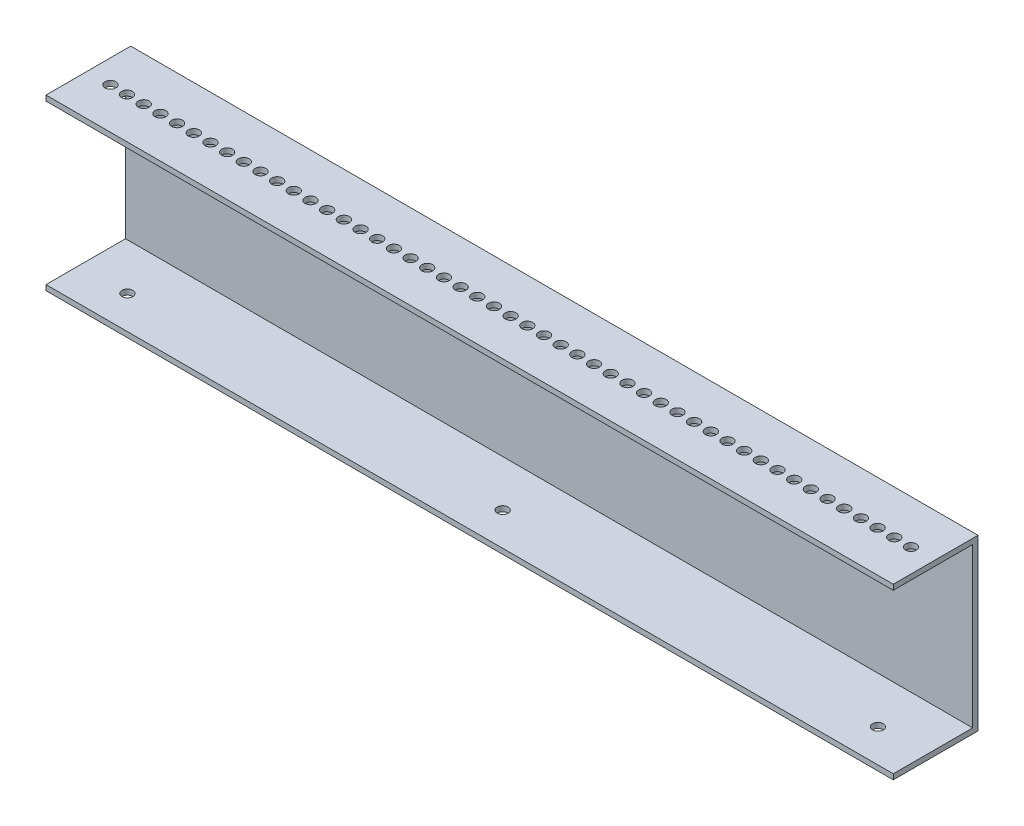
SolidWorks part; units mm, degrees
material "6061-T6 (SS)"
ref_plane "Front Plane" through (0, 0, 0) normal (0, 0, 1) x (1, 0, 0)
ref_plane "Top Plane" through (0, 0, 0) normal (0, 1, 0) x (1, 0, 0)
ref_plane "Right Plane" through (0, 0, 0) normal (1, 0, 0) x (0, 0, -1)
sketch "Sketch3" plane through (0, 0, 0) normal (1, 0, 0) x (0, 0, -1)
  line L0 (-304.8, 12.7) -> (-254, 12.7)
  line L2 (-254, 12.7) -> (-254, 114.3)
  line L4 (-254, 114.3) -> (-304.8, 114.3)
  line L5 (-304.8, 114.3) -> (-304.8, 111.125)
  line L6 (-304.8, 111.125) -> (-257.175, 111.125)
  line L8 (-257.175, 111.125) -> (-257.175, 15.875)
  line L10 (-257.175, 15.875) -> (-304.8, 15.875)
  line L11 (-304.8, 15.875) -> (-304.8, 12.7)
  line L12 (0, 0) -> (0, 191.5015) construction
  dimension "D1" = 50.8
  dimension "D2" = 3.175
  dimension "D3" = 12.7
  dimension "D4" = 254
  dimension "D5" = 3.175
  dimension "D6" = 3.175
  dimension "D7" = 50.8
  dimension "D8" = 101.6
extrude "Alum C chnl SHORT Boss-Extrude3" add sketch "Sketch3" along normal blind 254 and the other way blind 254 separate body
sketch "Sketch12" plane through (0, 15.875, 0) normal (0, 1, 0) x (1, 0, 0)
  line L0 (225, -285) -> (0, -285) construction
  line L1 (0, -285) -> (-225, -285) construction
  line L2 (0, 0) -> (0, -285) construction
  circle A0 centre (-225, -285) radius 3.25
  circle A1 centre (0, -285) radius 3.25
  circle A2 centre (225, -285) radius 3.25
  dimension "D2" = 450
  dimension "D3" = 6.5
  dimension "D1" = 285
extrude "Cut-Extrude9" cut sketch "Sketch12" against normal blind 3.175
sketch "Sketch8" plane through (0, 114.3, 0) normal (0, 1, 0) x (1, 0, 0)
  line L0 (0, 0) -> (0, 285.8) construction
  line L1 (0, 0) -> (0, -280.2) construction
  line L2 (-254, -254) -> (254, -254) construction
  circle A0 centre (0, -280.2) radius 3.25
  dimension "D4" = 6.5
  dimension "D1" = 26.2
extrude "Cut-Extrude5" cut sketch "Sketch8" against normal blind 20
pattern_linear "LPattern4" count 25 spacing 10 along (-1, 0, 0) of "Cut-Extrude5"
pattern_linear "LPattern3" count 25 spacing 10 along (1, 0, 0) of "Cut-Extrude5"
